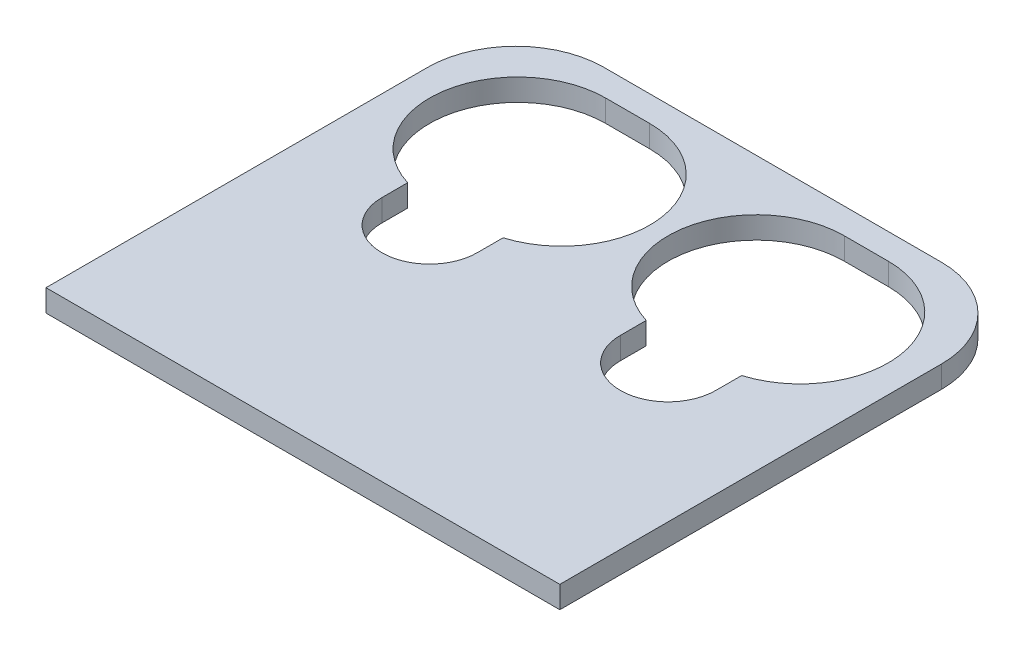
SolidWorks part; units mm, degrees
ref_plane "Front Plane" through (0, 0, 0) normal (0, 0, 1) x (1, 0, 0)
ref_plane "Top Plane" through (0, 0, 0) normal (0, 1, 0) x (1, 0, 0)
ref_plane "Right Plane" through (0, 0, 0) normal (1, 0, 0) x (0, 0, -1)
sketch "Sketch1" plane through (0, 0, 0) normal (0, 1, 0) x (1, 0, 0)
  line L1 (-35, -33.5) -> (35, -33.5)
  line L2 (-35, -33.5) -> (-35, 33.5)
  line L3 (-35, 33.5) -> (35, 33.5)
  line L4 (35, -33.5) -> (35, 33.5)
  line L5 (-35, -33.5) -> (35, 33.5) construction
  line L6 (-35, 33.5) -> (35, -33.5) construction
  point P0 (0, 0)
  dimension "D1" = 67
  dimension "D2" = 70
extrude "Boss-Extrude1" add sketch "Sketch1" along normal blind 3
sketch "Sketch5" plane through (0, 3, 0) normal (0, 1, 0) x (1, 0, 0)
  line L0 (35, -33.5) -> (35, 33.5) construction
  line L1 (-35, 33.5) -> (35, 33.5)
  line L2 (-35, 33.5) -> (-35, 30.5)
  line L3 (-35, 30.5) -> (35, 30.5)
  line L4 (35, 33.5) -> (35, 30.5)
  dimension "D1" = 3
extrude "Cut-Extrude4" cut sketch "Sketch5" against normal through all both and the other way through all
fillet "Fillet1" radius 12 2 edges at (35, 1.5, -30.5) (-35, 1.5, -30.5)
sketch "Sketch2" plane through (0, 3, 0) normal (0, 1, 0) x (1, 0, 0)
  circle A0 centre (-16.25, 0) radius 6.5
  dimension "D1" = 13
  dimension "D2" = 16.25
extrude "Cut-Extrude1" cut sketch "Sketch2" against normal through all both and the other way through all
ref_point "Point1"
sketch "Sketch3" plane through (0, 3, 0) normal (0, 1, 0) x (1, 0, 0)
  line L0 (-19.25, 15) -> (-13.25, 15) construction
  line L1 (-19.25, 27) -> (-13.25, 27)
  line L2 (-19.25, 3) -> (-13.25, 3)
  arc A1 (-19.25, 27) -> (-19.25, 3) centre (-19.25, 15) ccw
  arc A2 (-13.25, 3) -> (-13.25, 27) centre (-13.25, 15) ccw
  point P2 (-16.25, 15)
  dimension "D1" = 12
  dimension "D2" = 6
  dimension "D3" = 15
extrude "Cut-Extrude2" cut sketch "Sketch3" against normal through all both and the other way through all
sketch "Sketch4" plane through (0, 3, 0) normal (0, 1, 0) x (1, 0, 0)
  line L0 (-22.75, 0) -> (-9.75, 0)
  line L1 (-22.75, 0) -> (-22.75, 8.8281)
  line L2 (-9.75, 0) -> (-9.75, 8.8281)
  line L3 (-22.75, 8.8281) -> (-9.75, 8.8281)
  arc A0 (-21.8578, 3.2868) -> (-10.6422, 3.2868) centre (-16.25, 0) ccw construction
extrude "Cut-Extrude3" cut sketch "Sketch4" against normal through all both and the other way through all
mirror "Mirror1" about plane through (0, 0, 0) normal (1, 0, 0) of "Cut-Extrude3", "Cut-Extrude2", "Cut-Extrude1"
